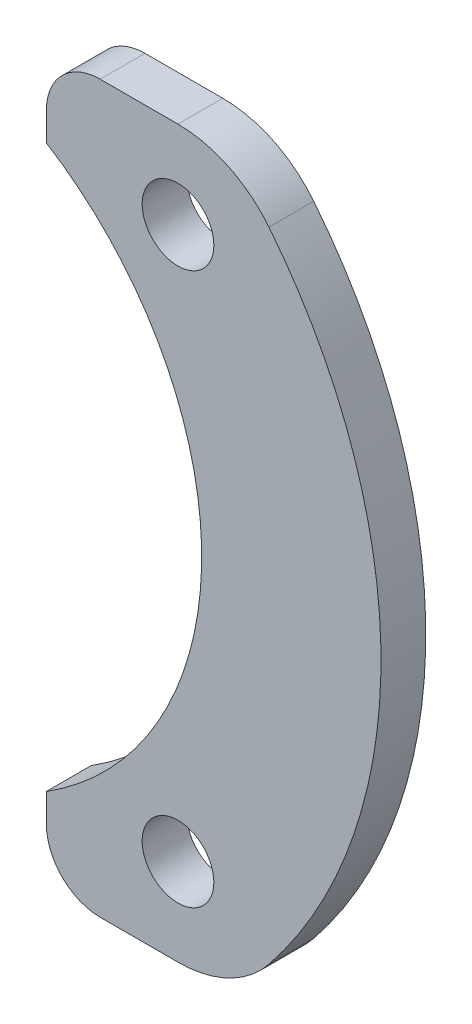
SolidWorks part; units mm, degrees
ref_plane "Front Plane" through (0, 0, 0) normal (0, 0, 1) x (1, 0, 0)
ref_plane "Top Plane" through (0, 0, 0) normal (0, 1, 0) x (1, 0, 0)
ref_plane "Right Plane" through (0, 0, 0) normal (1, 0, 0) x (0, 0, -1)
sketch "Sketch2" plane through (0, 0, 0) normal (0, 0, 1) x (1, 0, 0)
  line L0 (17.1778, 20.25) -> (12.8331, 20.25)
  line L1 (9.8331, 17.25) -> (9.8331, 15.6704)
  line L2 (9.8331, -15.6704) -> (9.8331, -17.25)
  line L3 (12.8331, -20.25) -> (17.1778, -20.25)
  line L8 (17.1778, 20.75) -> (12.8331, 20.75) construction
  line L9 (12.8331, -20.75) -> (17.1778, -20.75) construction
  line L10 (9.3331, -15.3914) -> (9.3331, -17.25) construction
  line L11 (9.3331, 17.25) -> (9.3331, 15.3914) construction
  arc A0 (12.8331, 20.25) -> (9.8331, 17.25) centre (12.8331, 17.25) ccw
  arc A1 (9.8331, -15.6704) -> (9.8331, 15.6704) centre (0, 0) ccw
  arc A2 (9.8331, -17.25) -> (12.8331, -20.25) centre (12.8331, -17.25) ccw
  arc A3 (17.1778, -20.25) -> (22.2523, -17.8119) centre (17.1778, -13.75) ccw
  arc A4 (22.2523, -17.8119) -> (22.2523, 17.8119) centre (0, 0) ccw
  arc A5 (22.2523, 17.8119) -> (17.1778, 20.25) centre (17.1778, 13.75) ccw
  arc A12 (22.6427, 18.1244) -> (17.1778, 20.75) centre (17.1778, 13.75) ccw construction
  arc A13 (22.6427, -18.1244) -> (22.6427, 18.1244) centre (0, 0) ccw construction
  arc A14 (17.1778, -20.75) -> (22.6427, -18.1244) centre (17.1778, -13.75) ccw construction
  arc A15 (9.3331, -17.25) -> (12.8331, -20.75) centre (12.8331, -17.25) ccw construction
  arc A16 (9.3331, -15.3914) -> (9.3331, 15.3914) centre (0, 0) ccw construction
  arc A17 (12.8331, 20.75) -> (9.3331, 17.25) centre (12.8331, 17.25) ccw construction
  circle A20 centre (17.1778, -15.3914) radius 2
  circle A21 centre (17.1778, 15.3914) radius 2
  dimension "D2" = 0.5
extrude "Boss-Extrude1" add sketch "Sketch2" along normal blind 2.5
sketch "Sketch3" plane through (0, 0, 2.5) normal (0, 0, 1) x (1, 0, 0)
  line L0 (18.5, 0) -> (28.5032, 0) construction
  arc A0 (9.8331, -15.6704) -> (9.8331, 15.6704) centre (0, 0) ccw construction
  arc A1 (22.2523, -17.8119) -> (22.2523, 17.8119) centre (0, 0) ccw construction
